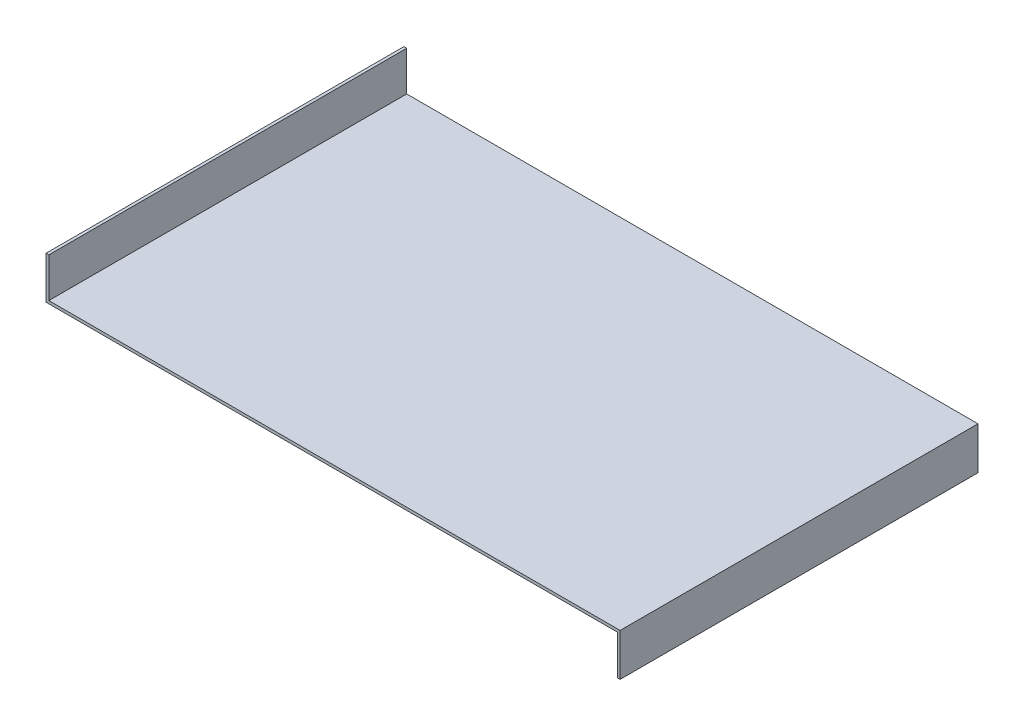
SolidWorks part; units mm, degrees
material "PPS"
ref_plane "Płaszczyzna XY" through (0, 0, 0) normal (0, 0, 1) x (1, 0, 0)
ref_plane "Płaszczyzna XZ" through (0, 0, 0) normal (0, 1, 0) x (1, 0, 0)
ref_plane "Płaszczyzna YZ" through (0, 0, 0) normal (1, 0, 0) x (0, 0, -1)
sketch "Szkic1" plane through (0, 0, 0) normal (0, 0, 1) x (1, 0, 0)
  line L0 (0, 0) -> (0, 15)
  line L1 (0, 15) -> (-202, 15)
  line L2 (-202, 15) -> (-202, 29)
  line L3 (-202, 29) -> (-203, 29)
  line L4 (-203, 29) -> (-203, 14)
  line L5 (-203, 14) -> (-1, 14)
  line L6 (-1, 14) -> (-1, 0)
  line L7 (-1, 0) -> (0, 0)
  dimension "D1" = 202
  dimension "D2" = 15
  dimension "D3" = 1
  dimension "D4" = 1
  dimension "D5" = 1
  dimension "D6" = 15
extrude "Dodanie-wyciągnięcie1" add sketch "Szkic1" along normal blind 126.55
